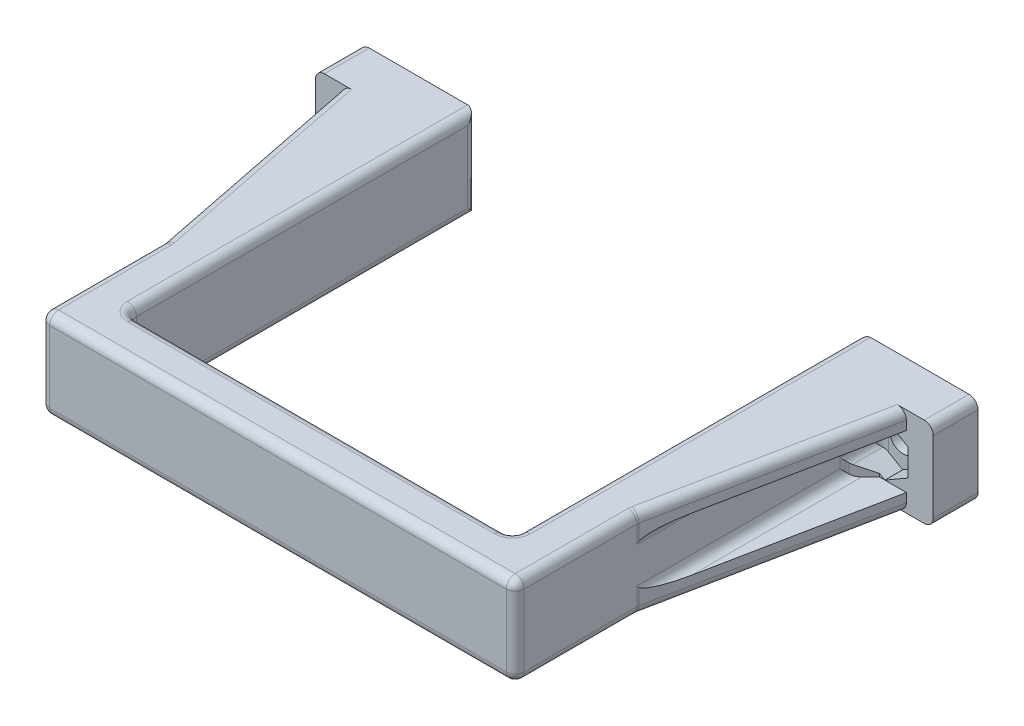
SolidWorks part; units mm, degrees
material "ABS"
ref_plane "Front Plane" through (0, 0, 0) normal (0, 0, 1) x (1, 0, 0)
ref_plane "Top Plane" through (0, 0, 0) normal (0, 1, 0) x (1, 0, 0)
ref_plane "Right Plane" through (0, 0, 0) normal (1, 0, 0) x (0, 0, -1)
sketch "Sketch1" plane through (0, 0, 0) normal (0, 1, 0) x (1, 0, 0)
  line L0 (0, -1000) -> (0, 49000) construction
  line L1 (-21.5, -19.5) -> (21.5, -19.5)
  line L2 (-21.5, -19.5) -> (-21.5, 19.5)
  line L3 (-21.5, 19.5) -> (21.5, 19.5) construction
  line L4 (21.5, -19.5) -> (21.5, 19.5)
  line L5 (-21.5, -19.5) -> (21.5, 19.5) construction
  line L6 (-21.5, 19.5) -> (21.5, -19.5) construction
  line L7 (-34.5, 19.5) -> (34.5, 19.5)
  line L8 (-34.5, 19.5) -> (-34.5, 14.5)
  line L9 (-34.5, 14.5) -> (-26.5, 14.5)
  line L10 (34.5, 19.5) -> (34.5, 14.5)
  line L11 (-21.5, 14.5) -> (21.5, 14.5) construction
  line L12 (-26.5, 14.5) -> (-26.5, -24.188)
  line L13 (-26.5, -24.188) -> (26.5, -24.188)
  line L14 (26.5, 14.5) -> (26.5, -24.188)
  line L15 (-21.5, 14.5) -> (21.5, 14.5) construction
  line L16 (26.5, 14.5) -> (34.5, 14.5)
  point P0 (0, 0)
  point P16 (-42.448, 19.5)
  dimension "D1" = 43
  dimension "D2" = 39
  dimension "D3" = 5
  dimension "D4" = 5
  dimension "D5" = 8
extrude "Boss-Extrude1" add sketch "Sketch1" along normal mid plane 10 contours L14 L16 L10 L7 L4 L1 L2 L8 L9 L12 L13
sketch "Sketch2" plane through (0, 0, -14.5) normal (0, 0, 1) x (1, 0, 0)
  line L0 (-26.5, 5) -> (-26.5, -5) construction
  line L1 (-26.5, 1.5011) -> (-29.1, 3.0022)
  line L2 (-29.1, 3.0022) -> (-31.7, 1.5011)
  line L3 (-31.7, 1.5011) -> (-31.7, -1.5011)
  line L4 (-31.7, -1.5011) -> (-29.1, -3.0022)
  line L5 (-29.1, -3.0022) -> (-26.5, -1.5011)
  line L6 (-26.5, -1.5011) -> (-26.5, 1.5011)
  line L7 (-34.5, 5) -> (-34.5, -5) construction
  circle A0 centre (-29.1, 0) radius 2.6 construction
  point P14 (-34.5, 0)
  dimension "D1" = 5.2
extrude "Cut-Extrude1" cut sketch "Sketch2" against normal blind 2
sketch "Sketch3" plane through (0, 0, -16.5) normal (0, 0, 1) x (1, 0, 0)
  point P0 (-29.1, 0)
hole_wizard "M2.5 Clearance Hole1" positions "Sketch3" profile "Sketch4" hole size "M2.5" standard "ANSI Metric" end condition through all
sketch "Sketch4" plane through (-29.1, 0, -16.5) normal (1, 0, 0) x (0, -1, 0)
  line L0 (0, 0) -> (0, 3)
  line L1 (0, 3) -> (1.45, 3)
  line L2 (1.45, 3) -> (1.45, 0)
  line L5 (1.45, 0) -> (0, 0)
  line L11 (0, -6.35) -> (0, 107.95) construction
  dimension "Thru Hole Dia." = 2.9
  dimension "Thru Hole Depth" = 3
sketch "Sketch5" plane through (0, 5, 0) normal (0, 1, 0) x (1, 0, 0)
  line L0 (-31.5, 14.5) -> (-26.5, -10.5)
  line L2 (-26.5, 14.5) -> (-26.5, -24.188) construction
  line L3 (-34.5, 14.5) -> (-26.5, 14.5) construction
  point P6 (0, 0)
  point P7 (-32.8288, 14.5)
  point P8 (-26.5, 8.5)
  point P9 (-31.0772, 14.5)
  dimension "D1" = 5
  dimension "D2" = 25
rib "Rib1" sketch "Sketch5" sketch "Sketch5" thickness 2 extrusion direction parallel to sketch draft on no parameters "D1"=2
mirror "Mirror1" about plane through (0, 0, 0) normal (0, 1, 0) of "Rib1"
mirror "Mirror2" about plane through (0, 0, 0) normal (1, 0, 0) of "Cut-Extrude1", "M2.5 Clearance Hole1", "Rib1", "Mirror1"
chamfer "Chamfer1" distance 2 angle 45 4 edges at (26.5, -2.2506, -14.5) (26.5, 2.2506, -14.5) (-26.5, -2.2506, -14.5) (-26.5, 2.2506, -14.5)
fillet "Fillet1" radius 1 44 edges at (-29, 5, -2) (-29, -5, -2) (29, -5, -2) (29, 5, -2) (0, -5, 19.5) (0, 5, 19.5) (-26.5, 0, -16.5) (-26.5, 1.5011, -14.5) (-26.5, 2.2506, -12.5) (-26.5, 3, -1) (-26.5, 4, 10.5) (-26.5, 5, 17.344) (-26.5, -5, 17.344) (-26.5, -4, 10.5) (-26.5, -3, -1) (-26.5, -2.2506, -12.5) (-26.5, -1.5011, -14.5) (26.5, -4, 10.5) (26.5, -5, 17.344) (26.5, 5, 17.344) (26.5, 4, 10.5) (26.5, 3, -1) (26.5, 2.2506, -12.5) (26.5, 1.5011, -14.5) (26.5, 0, -16.5) (26.5, -1.5011, -14.5) (26.5, -2.2506, -12.5) (26.5, -3, -1) (-26.5, 0, 24.188) (0, -5, 24.188) (0, 5, 24.188) (26.5, 0, 24.188) (21.5, 0, -19.5) (21.5, -5, 0) (21.5, 5, 0) (21.5, 0, 19.5) (-21.5, 0, 19.5) (-21.5, -5, 0) (-21.5, 5, 0) (-21.5, 0, -19.5) (-34.5, -5, -17) (-34.5, 5, -17) (34.5, -5, -17) (34.5, 5, -17)
